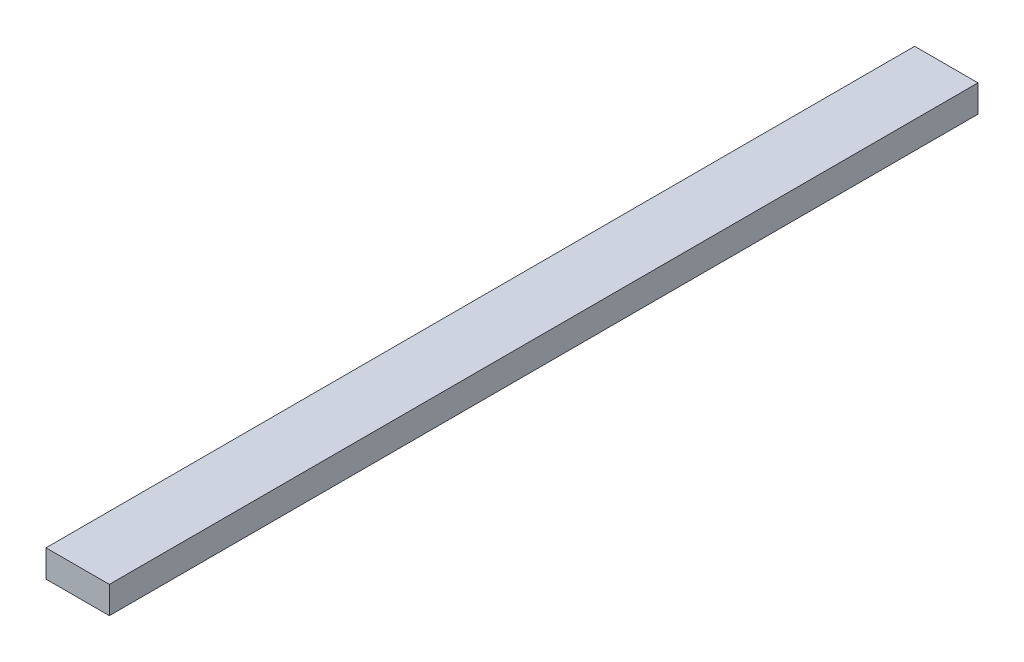
SolidWorks part; units mm, degrees
material "Pine"
ref_plane "Front Plane" through (0, 0, 0) normal (0, 0, 1) x (1, 0, 0)
ref_plane "Top Plane" through (0, 0, 0) normal (0, 1, 0) x (1, 0, 0)
ref_plane "Right Plane" through (0, 0, 0) normal (1, 0, 0) x (0, 0, -1)
sketch "Sketch1" plane through (0, 0, 0) normal (0, 0, 1) x (1, 0, 0)
  line L1 (-26.1179, 29.2993) -> (62.7821, 29.2993)
  line L2 (-26.1179, 29.2993) -> (-26.1179, -8.8007)
  line L3 (-26.1179, -8.8007) -> (62.7821, -8.8007)
  line L4 (62.7821, 29.2993) -> (62.7821, -8.8007)
  dimension "D1" = 88.9
  dimension "D2" = 38.1
extrude "Boss-Extrude1" add sketch "Sketch1" along normal blind 1219.2
